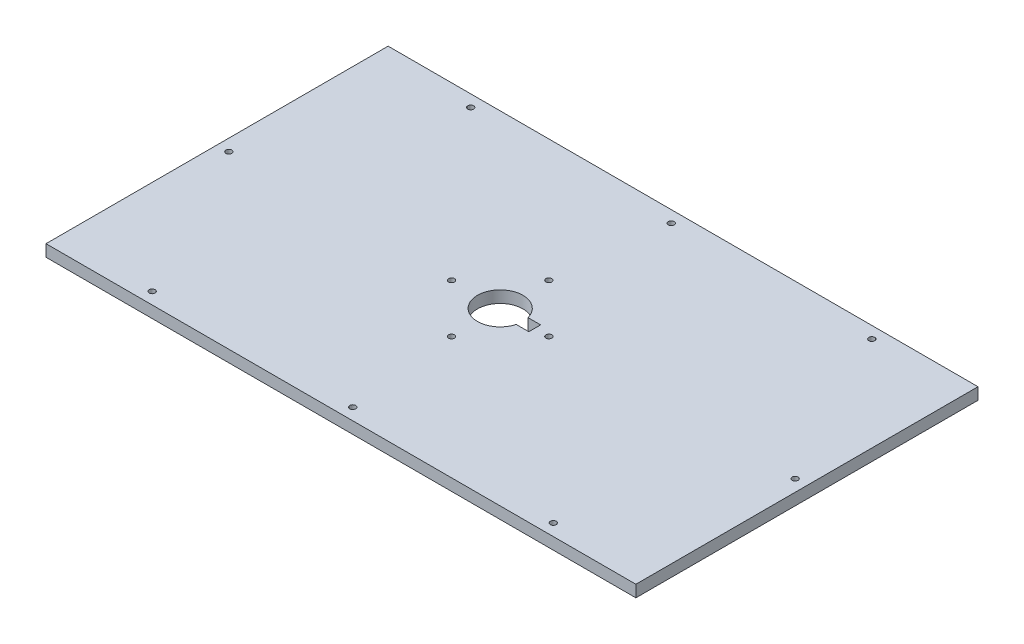
SolidWorks part; units mm, degrees
material "Acrylic (Medium-high impact)"
ref_plane "Front Plane" through (0, 0, 0) normal (0, 0, 1) x (1, 0, 0)
ref_plane "Top Plane" through (0, 0, 0) normal (0, 1, 0) x (1, 0, 0)
ref_plane "Right Plane" through (0, 0, 0) normal (1, 0, 0) x (0, 0, -1)
sketch "Sketch1" plane through (0, 0, 0) normal (0, 1, 0) x (1, 0, 0)
  line L0 (-30.5222, -17.7029) -> (250, 145) construction
  line L1 (-250, -145) -> (250, -145)
  line L2 (-250, -145) -> (-250, 145)
  line L3 (-250, 145) -> (250, 145)
  line L4 (250, -145) -> (250, 145)
  line L5 (-250, -145) -> (-232.7586, -135) construction
  line L6 (-250, 145) -> (250, -145) construction
  line L7 (-240, -135) -> (240, -135) construction
  line L8 (-240, -135) -> (-240, 135) construction
  line L9 (-240, 135) -> (240, 135) construction
  line L10 (240, -135) -> (240, 135) construction
  line L12 (-240, 135) -> (240, -135) construction
  line L13 (-317.3233, 0) -> (323.4582, 0) construction
  line L14 (8.5893, -5) -> (19.25, -5)
  line L16 (8.5893, 5) -> (19.25, 5)
  line L17 (19.25, -5) -> (19.25, 5)
  circle A0 centre (-240, 0) radius 2.5
  circle A1 centre (-10, 0) radius 41.25 construction
  circle A2 centre (-170, -135) radius 2.5
  circle A3 centre (-170, 135) radius 2.5
  circle A4 centre (170, 135) radius 2.5
  circle A5 centre (240, 0) radius 2.5
  circle A6 centre (170, -135) radius 2.5
  circle A7 centre (0, 135) radius 2.5
  circle A8 centre (0, -135) radius 2.5
  circle A9 centre (31.25, 0) radius 2.5
  circle A10 centre (-10, -41.25) radius 2.5
  circle A11 centre (-51.25, 0) radius 2.5
  circle A12 centre (-10, 41.25) radius 2.5
  arc A13 (8.5893, 5) -> (8.5893, -5) centre (-10, 0) ccw
  point P13 (9.25, 0)
  point P38 (-67.7803, 0)
  point P47 (-10, 0)
  dimension "D7" = 5
  dimension "D8" = 5
  dimension "D9" = 5
  dimension "D10" = 5
  dimension "D11" = 145
  dimension "D12" = 5
  dimension "D13" = 5
  dimension "D14" = 5
  dimension "D15" = 5
  dimension "D22" = 480
  dimension "D23" = 270
  dimension "D25" = 5
  dimension "D26" = 4
  dimension "D27" = 38.5
  dimension "D29" = 10
  dimension "D30" = 240
  dimension "D28" = 10
  dimension "D24" = 82.5
  dimension "D1" = 290
  dimension "D2" = 500
  dimension "D3" = 10
  dimension "D4" = 10
  dimension "D5" = 250
  dimension "D6" = 145
  dimension "D16" = 80
  dimension "D17" = 80
  dimension "D18" = 80
  dimension "D19" = 80
  dimension "D20" = 250
  dimension "D21" = 250
extrude "Boss-Extrude1" add sketch "Sketch1" along normal blind 10
